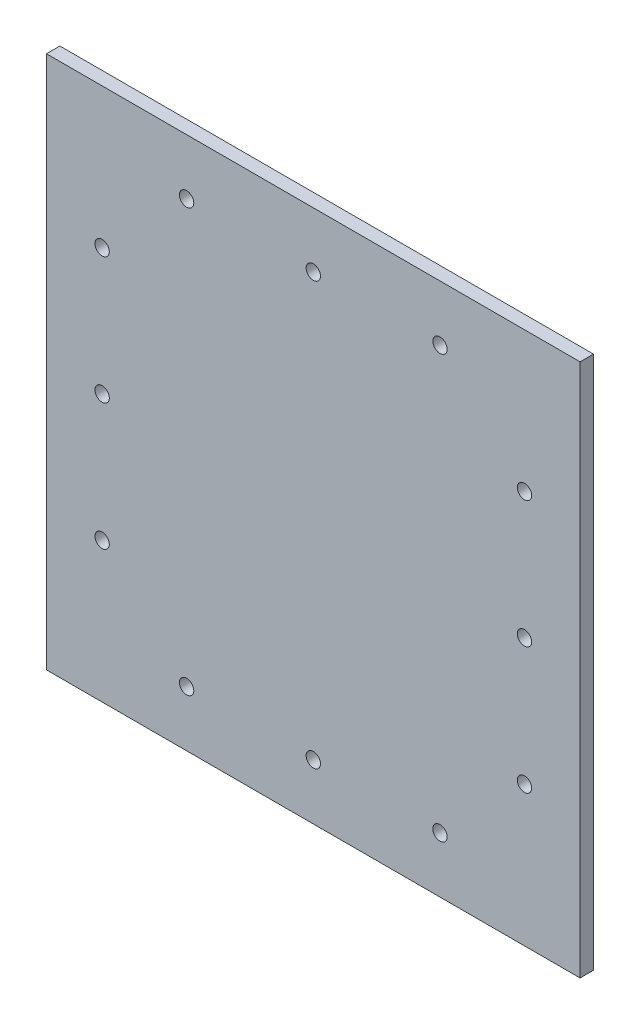
SolidWorks part; units mm, degrees
material "Acrylic (Medium-high impact)"
ref_plane "Front Plane" through (0, 0, 0) normal (0, 0, 1) x (1, 0, 0)
ref_plane "Top Plane" through (0, 0, 0) normal (0, 1, 0) x (1, 0, 0)
ref_plane "Right Plane" through (0, 0, 0) normal (1, 0, 0) x (0, 0, -1)
sketch "Sketch1" plane through (0, 0, 0) normal (0, 0, 1) x (1, 0, 0)
  line L1 (-63.175, -63.175) -> (63.175, -63.175)
  line L2 (-63.175, -63.175) -> (-63.175, 63.175)
  line L3 (-63.175, 63.175) -> (63.175, 63.175)
  line L4 (63.175, -63.175) -> (63.175, 63.175)
  line L5 (-63.175, -63.175) -> (63.175, 63.175) construction
  line L6 (-63.175, 63.175) -> (63.175, -63.175) construction
  point P0 (0, 0)
  dimension "D1" = 126.35
  dimension "D2" = 126.35
extrude "Boss-Extrude1" add sketch "Sketch1" along normal blind 3.175 contours L3 L4 L1 L2
extrude "Cut-Extrude1" cut sketch "Sketch2" against normal blind 7
sketch "Sketch2" plane through (-17.0478, -31.682, 0) normal (0, 0, -1) x (-1, 0, 0)
  line L0 (-80.2228, 94.857) -> (46.1272, -31.493) construction
  line L1 (46.1272, 94.857) -> (-80.2228, -31.493) construction
  circle A15 centre (-17.0478, -18.318) radius 1.7
  circle A16 centre (12.9522, -18.318) radius 1.7
  circle A17 centre (-47.0478, -18.318) radius 1.7
  circle A18 centre (-67.0478, 61.682) radius 1.7
  circle A19 centre (-67.0478, 31.682) radius 1.7
  circle A20 centre (-67.0478, 1.682) radius 1.7
  circle A21 centre (12.9522, 81.682) radius 1.7
  circle A22 centre (-17.0478, 81.682) radius 1.7
  circle A23 centre (-47.0478, 81.682) radius 1.7
  circle A24 centre (32.9522, 1.682) radius 1.7
  circle A25 centre (32.9522, 31.682) radius 1.7
  circle A26 centre (32.9522, 61.682) radius 1.7
  point P10 (-17.0478, 31.682)
  point P32 (-17.0478, 31.682)
